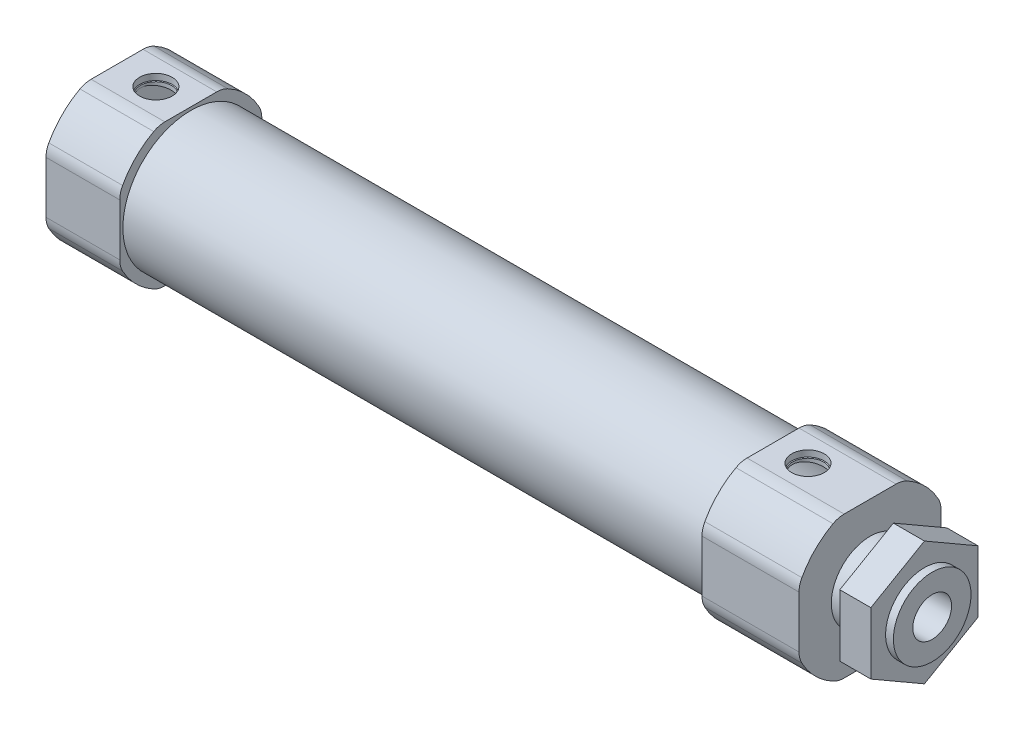
SolidWorks part; units mm, degrees
material "6061-T6 (SS)"
ref_plane "前视基准面" through (0, 0, 0) normal (0, 0, 1) x (1, 0, 0)
ref_plane "上视基准面" through (0, 0, 0) normal (0, 1, 0) x (1, 0, 0)
ref_plane "右视基准面" through (0, 0, 0) normal (1, 0, 0) x (0, 0, -1)
sketch "主筒" plane through (0, 0, 0) normal (1, 0, 0) x (0, 0, -1)
  circle A0 centre (0, 0) radius 8.75
  dimension "D1" = 17.5
extrude "主缸筒" add sketch "主筒" along normal blind 97
sketch "前头1" plane through (97, 0, 0) normal (1, 0, 0) x (0, 0, -1)
  line L1 (-9.15, 9.15) -> (9.15, 9.15)
  line L2 (-9.15, 9.15) -> (-9.15, -9.15)
  line L3 (-9.15, -9.15) -> (9.15, -9.15)
  line L4 (9.15, 9.15) -> (9.15, -9.15)
  line L5 (-9.15, 9.15) -> (9.15, -9.15) construction
  line L6 (-9.15, -9.15) -> (9.15, 9.15) construction
  circle A0 centre (0, 0) radius 10
  point P0 (0, 0)
  circle M3 centre (0, 0) radius 8.75
  dimension "D2" = 20
  dimension "D1" = 18.3
extrude "前头" add sketch "前头1" against normal blind 12.5 contours L2 A0 L3 M3
sketch "后头1" plane through (0, 0, 0) normal (-1, 0, 0) x (0, 0, 1)
  line L1 (-9.15, 9.15) -> (9.15, 9.15)
  line L2 (-9.15, 9.15) -> (-9.15, -9.15)
  line L3 (-9.15, -9.15) -> (9.15, -9.15)
  line L4 (9.15, 9.15) -> (9.15, -9.15)
  line L5 (-9.15, 9.15) -> (9.15, -9.15) construction
  line L6 (-9.15, -9.15) -> (9.15, 9.15) construction
  circle A0 centre (0, 0) radius 10
  point P0 (0, 0)
  circle M9 centre (0, 0) radius 8.75
  dimension "D2" = 20
  dimension "D1" = 18.3
extrude "后头" add sketch "后头1" against normal blind 9.5 contours L4 A0 L1 L2 L3 M9
sketch "气管接头1" plane through (0, 9.15, 0) normal (0, 1, 0) x (1, 0, 0)
  line L0 (0, 0) -> (97, 0) construction
  line L1 (97, -4.0345) -> (97, 4.0345) construction
  line L2 (0, 4.0345) -> (0, -4.0345) construction
  circle A0 centre (5, 0) radius 2
  circle A1 centre (89, 0) radius 2
  dimension "D1" = 5
  dimension "D3" = 4
  dimension "D2" = 8
extrude "气管接头" cut sketch "气管接头1" against normal blind 10
hole_wizard "外孔" positions "3D草图1" profile "草图5" tap size "M5" standard "GB"
sketch3d "3D草图1"
  point P0 (5, 9.15, 0)
  point P3 (89, 9.15, 0)
sketch "草图5" plane through (5, 9.15, 0) normal (1, 0, 0) x (0, 0, 1)
  line L0 (0, 0) -> (0, 2.0618)
  line L1 (0, 2.0618) -> (2.1, 0.8)
  line L2 (2.1, 0.8) -> (2.1, 0)
  line L5 (2.1, 0) -> (0, 0)
  line L10 (0, 2.0618) -> (-2.1, 0.8) construction
  line L11 (0, -6.35) -> (0, 107.95) construction
  dimension "螺纹孔钻头直径" = 4.2
  dimension "螺纹孔钻头深度" = 0.8
  dimension "导头角度" = 118
cosmetic thread "孔螺蚊线1" parameters "D1"=0.8, "D2"=5
cosmetic thread "孔螺蚊线3" parameters "D1"=0.8, "D2"=5
sketch "内腔1" plane through (97, 0, 0) normal (1, 0, 0) x (0, 0, -1)
  circle A0 centre (0, 0) radius 8
  dimension "D1" = 16
extrude "切除-拉伸3" cut sketch "内腔1" against normal offset from surface (91 mm away) 3 from offset 3 up to face at (0, 0, 0) offset against normal yes
sketch "气缸头1" plane through (97, 0, 0) normal (1, 0, 0) x (0, 0, -1)
  circle A0 centre (0, 0) radius 5
  dimension "D1" = 10
extrude "气缸头" add sketch "气缸头1" along normal blind 8
cosmetic thread "装饰螺纹线1" parameters "D1"=5, "D2"=6.647
sketch "内芯1" plane through (105, 0, 0) normal (1, 0, 0) x (0, 0, -1)
  circle A0 centre (0, 0) radius 2.5
  dimension "D1" = 5
extrude "内芯" cut sketch "内芯1" against normal up to next
fillet "圆角2" radius 3 8 edges at (4.75, -4.0345, 9.15) (4.75, 4.0345, 9.15) (4.75, 4.0345, -9.15) (4.75, -4.0345, -9.15) (4.75, -9.15, -4.0345) (4.75, -9.15, 4.0345) (4.75, 9.15, 4.0345) (4.75, 9.15, -4.0345)
fillet "圆角3" radius 3 8 edges at (90.75, -4.0345, -9.15) (90.75, 4.0345, -9.15) (90.75, 9.15, -4.0345) (90.75, 9.15, 4.0345) (90.75, 4.0345, 9.15) (90.75, -4.0345, 9.15) (90.75, -9.15, 4.0345) (90.75, -9.15, -4.0345)
sketch "草图6" plane through (97, 0, 0) normal (1, 0, 0) x (0, 0, -1)
  line L1 (0, -7.9674) -> (6.9, -3.9837)
  line L2 (6.9, -3.9837) -> (6.9, 3.9837)
  line L3 (6.9, 3.9837) -> (0, 7.9674)
  line L4 (0, 7.9674) -> (-6.9, 3.9837)
  line L5 (-6.9, 3.9837) -> (-6.9, -3.9837)
  line L6 (-6.9, -3.9837) -> (0, -7.9674)
  circle A0 centre (0, 0) radius 6.9 construction
  circle A1 centre (0, 0) radius 5 construction
  circle A2 centre (0, 0) radius 5
  dimension "D1" = 13.8
extrude "凸台-拉伸1" add sketch "草图6" along normal blind 4 from offset 3 separate body
equation "\"行程l\"= 50"
equation "\"D1@主缸筒\"=\"行程l\"+47"
equation "\"行程2\"= 200"
